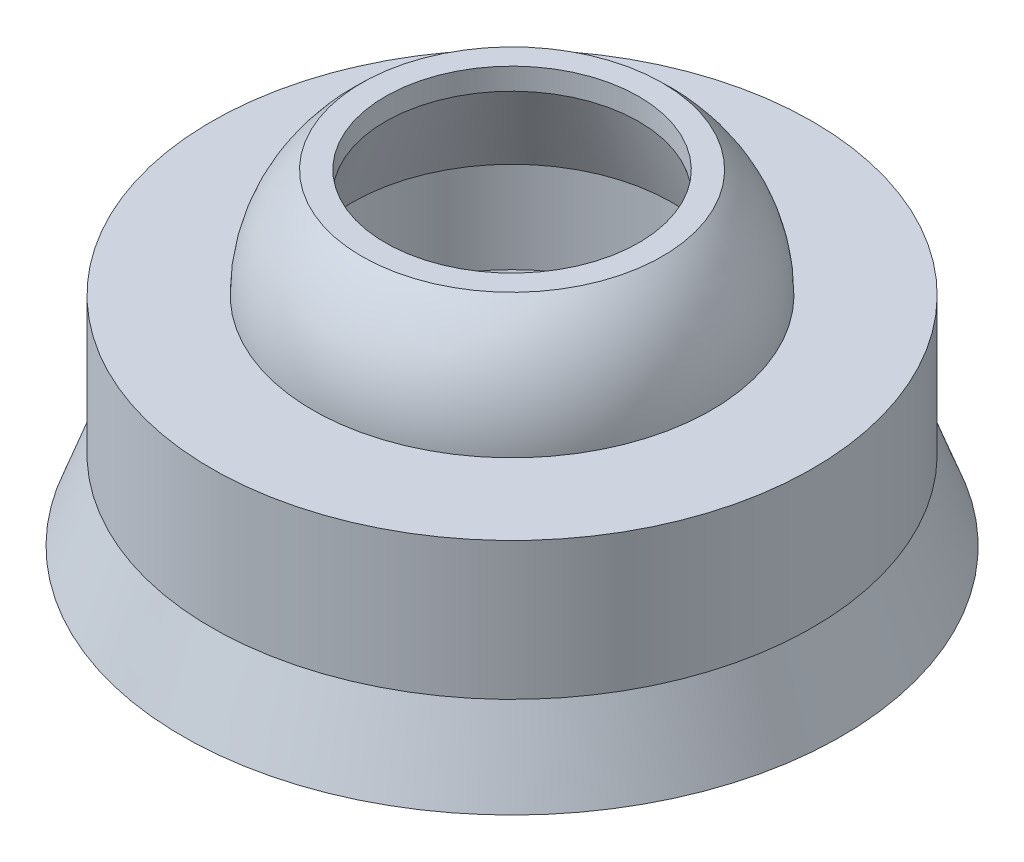
SolidWorks part; units mm, degrees
ref_plane "Front Plane" through (0, 0, 0) normal (0, 0, 1) x (1, 0, 0)
ref_plane "Top Plane" through (0, 0, 0) normal (0, 1, 0) x (1, 0, 0)
ref_plane "Right Plane" through (0, 0, 0) normal (1, 0, 0) x (0, 0, -1)
sketch "Sketch2" plane through (0, 0, 0) normal (1, 0, 0) x (0, 0, -1)
  line L0 (0, 0) -> (0, 1975.9377) construction
  line L1 (0, 0) -> (1975.9377, 0) construction
  line L2 (-4.15, -1.9) -> (-4.15, 0)
  line L3 (-4.15, 0) -> (-2.7521, 0)
  line L4 (-2.075, 1.5) -> (-1.75, 1.5)
  line L5 (-1.75, 1.5) -> (-1.75, 1.2)
  line L6 (-1.75, 1.2) -> (-2.2119, 0)
  line L7 (-2.2119, 0) -> (-2.2119, -1.26)
  line L8 (-2.2119, -1.26) -> (-1.75, -2.13)
  line L9 (-1.75, -2.13) -> (-2.25, -2.63)
  line L10 (-2.25, -2.63) -> (-2.85, -1.5)
  line L11 (-2.85, -1.5) -> (-3.3, -1.5)
  line L12 (-3.3, -1.5) -> (-3.85, -3)
  line L14 (-4.15, -1.9) -> (-4.55, -3)
  line L15 (-4.55, -3) -> (-3.85, -3)
  arc A0 (-2.7521, 0) -> (-2.075, 1.5) centre (-0.7521, 0) cw
  dimension "D8" = 1.26
  dimension "D20" = 4.15
  dimension "D1" = 1.5
  dimension "D2" = 1.5
  dimension "D3" = 3
  dimension "D4" = 1.1
  dimension "D5" = 0.3
  dimension "D6" = 1.2
  dimension "D7" = 2
  dimension "D9" = 0.87
  dimension "D10" = 0.5
  dimension "D11" = 0.37
  dimension "D12" = 8.3
  dimension "D13" = 9.1
  dimension "D14" = 7.7
  dimension "D15" = 6.6
  dimension "D16" = 5.7
  dimension "D17" = 4.5
  dimension "D18" = 3.5
  dimension "D19" = 3.5
revolve "Revolve1" add sketch "Sketch2" angle 360 about L0
